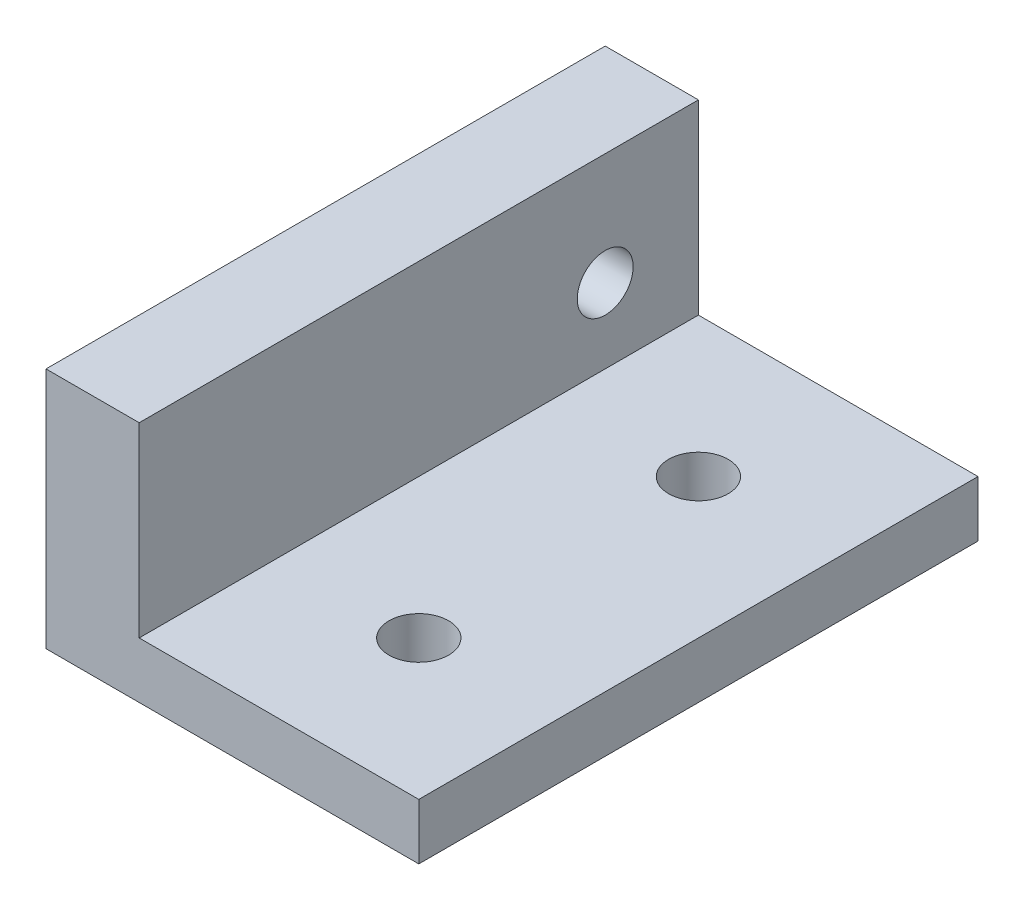
SolidWorks part; units mm, degrees
ref_plane "Front Plane" through (0, 0, 0) normal (0, 0, 1) x (1, 0, 0)
ref_plane "Top Plane" through (0, 0, 0) normal (0, 1, 0) x (1, 0, 0)
ref_plane "Right Plane" through (0, 0, 0) normal (1, 0, 0) x (0, 0, -1)
sketch "Sketch1" plane through (0, 0, 0) normal (0, 1, 0) x (1, 0, 0)
  line L1 (-10, 15) -> (10, 15)
  line L2 (-10, 15) -> (-10, -15)
  line L3 (-10, -15) -> (10, -15)
  line L4 (10, 15) -> (10, -15)
  line L5 (-10, 15) -> (10, -15) construction
  line L6 (-10, -15) -> (10, 15) construction
  point P0 (0, 0)
  dimension "D1" = 20
  dimension "D2" = 30
extrude "Boss-Extrude1" add sketch "Sketch1" along normal blind 3
sketch "Sketch2" plane through (0, 3, 0) normal (0, 1, 0) x (1, 0, 0)
  line L0 (-10, -15) -> (10, -15) construction
  line L1 (-10, 15) -> (-5, 15)
  line L2 (-10, 15) -> (-10, -15)
  line L3 (-10, -15) -> (-5, -15)
  line L4 (-5, 15) -> (-5, -15)
  dimension "D1" = 5
extrude "Boss-Extrude2" add sketch "Sketch2" along normal blind 10
sketch "Sketch3" plane through (-10, 0, 0) normal (-1, 0, 0) x (0, 0, 1)
  line L0 (-15, 7) -> (15, 7) construction
  line L1 (-15, 13) -> (-15, 0) construction
  line L2 (15, 13) -> (15, 0) construction
  line L4 (-15, 0) -> (15, 0) construction
  circle A0 centre (-10, 7) radius 1.5
  dimension "D2" = 5
  dimension "D3" = 3
  dimension "D1" = 7
extrude "Cut-Extrude1" cut sketch "Sketch3" against normal blind 10
sketch "Sketch4" plane through (0, 3, 0) normal (0, 1, 0) x (1, 0, 0)
  line L1 (-5, -15) -> (10, -15) construction
  line L2 (10, 15) -> (-5, 15) construction
  line L3 (10, -15) -> (10, 15) construction
  circle A0 centre (2.5, -7.5) radius 1.6
  circle A1 centre (2.5, 7.5) radius 1.6
  dimension "D1" = 3.2
  dimension "D2" = 3.2
  dimension "D3" = 7.5
  dimension "D4" = 7.5
  dimension "D5" = 7.5
  dimension "D6" = 7.5
extrude "Cut-Extrude2" cut sketch "Sketch4" against normal through all
